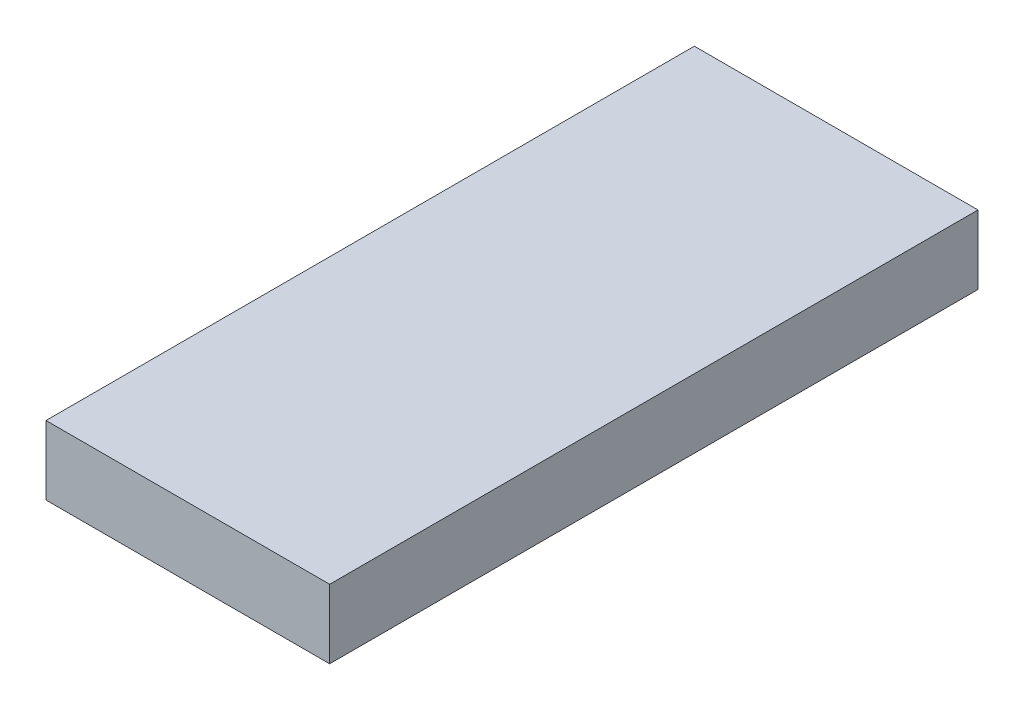
SolidWorks part; units mm, degrees
material "Acier inoxydable (ferritique)"
ref_plane "Plan de face" through (0, 0, 0) normal (0, 0, 1) x (1, 0, 0)
ref_plane "Plan de dessus" through (0, 0, 0) normal (0, 1, 0) x (1, 0, 0)
ref_plane "Plan de droite" through (0, 0, 0) normal (1, 0, 0) x (0, 0, -1)
sketch "Esquisse1" plane through (0, 0, 0) normal (0, 0, 1) x (1, 0, 0)
  line L1 (-3.5, 0) -> (3.5, 0)
  line L2 (-3.5, 0) -> (-3.5, 1.7)
  line L3 (-3.5, 1.7) -> (3.5, 1.7)
  line L4 (3.5, 0) -> (3.5, 1.7)
  dimension "D1" = 7
  dimension "D2" = 1.7
extrude "Extrusion1" add sketch "Esquisse1" along normal blind 16
